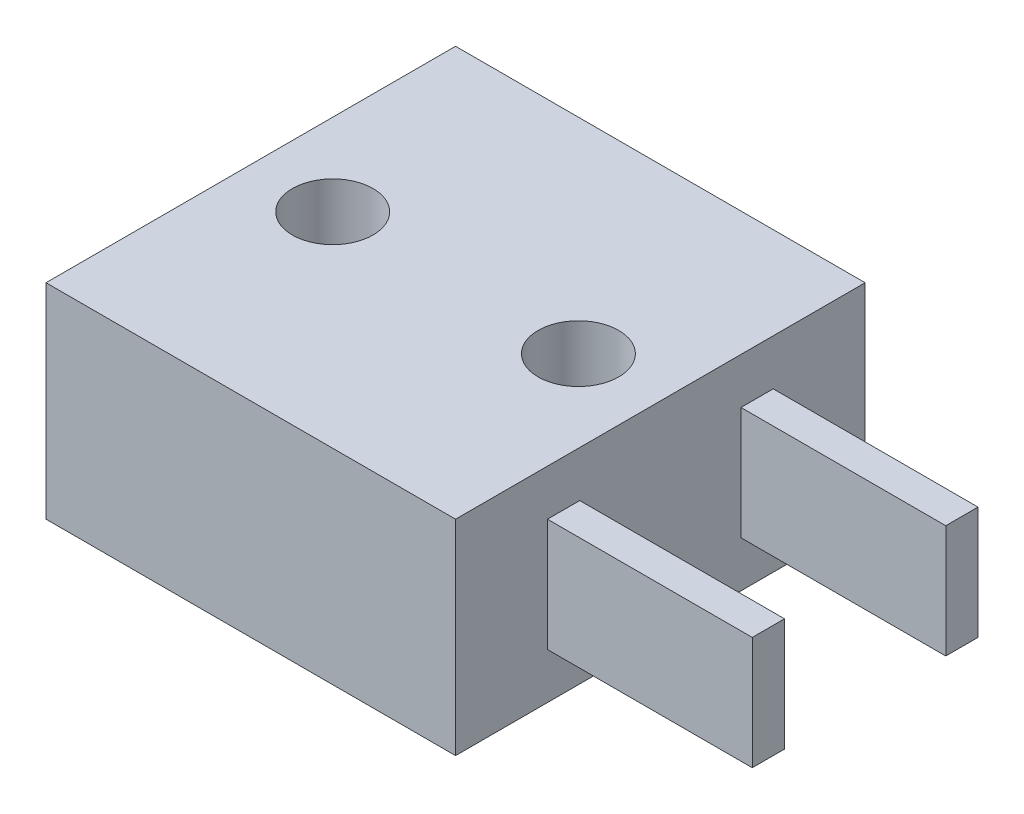
SolidWorks part; units mm, degrees
ref_plane "Front Plane" through (0, 0, 0) normal (0, 0, 1) x (1, 0, 0)
ref_plane "Top Plane" through (0, 0, 0) normal (0, 1, 0) x (1, 0, 0)
ref_plane "Right Plane" through (0, 0, 0) normal (1, 0, 0) x (0, 0, -1)
sketch "Sketch1" plane through (0, 0, 0) normal (0, 1, 0) x (1, 0, 0)
  line L0 (3.81, 0) -> (-3.81, 0) construction
  line L1 (-6.35, 6.35) -> (6.35, 6.35)
  line L2 (-6.35, 6.35) -> (-6.35, -6.35)
  line L3 (-6.35, -6.35) -> (6.35, -6.35)
  line L4 (6.35, 6.35) -> (6.35, -6.35)
  line L5 (-6.35, 6.35) -> (6.35, -6.35) construction
  line L6 (-6.35, -6.35) -> (6.35, 6.35) construction
  circle A0 centre (-3.81, 0) radius 1.25
  circle A1 centre (3.81, 0) radius 1.25
  point P0 (0, 0)
  point P11 (0, 0)
  dimension "D2" = 2.5
  dimension "D1" = 12.7
  dimension "D3" = 7.62
extrude "Boss-Extrude1" add sketch "Sketch1" along normal mid plane 6.35
sketch "Sketch2" plane through (0, 0, 0) normal (0, 1, 0) x (1, 0, 0)
  line L0 (6.35, -6.35) -> (6.35, 6.35) construction
  line L1 (6.35, 3.5) -> (12.7, 3.5)
  line L2 (6.35, 3.5) -> (6.35, 2.5)
  line L3 (6.35, 2.5) -> (12.7, 2.5)
  line L4 (12.7, 3.5) -> (12.7, 2.5)
  line L5 (0, 0) -> (13.0255, 0) construction
  line L6 (12.7, -3.5) -> (12.7, -2.5)
  line L7 (6.35, -2.5) -> (12.7, -2.5)
  line L8 (6.35, -3.5) -> (6.35, -2.5)
  line L9 (6.35, -3.5) -> (12.7, -3.5)
  dimension "D1" = 1
  dimension "D2" = 6.35
  dimension "D3" = 6
extrude "Boss-Extrude2" add sketch "Sketch2" along normal mid plane 3.5
